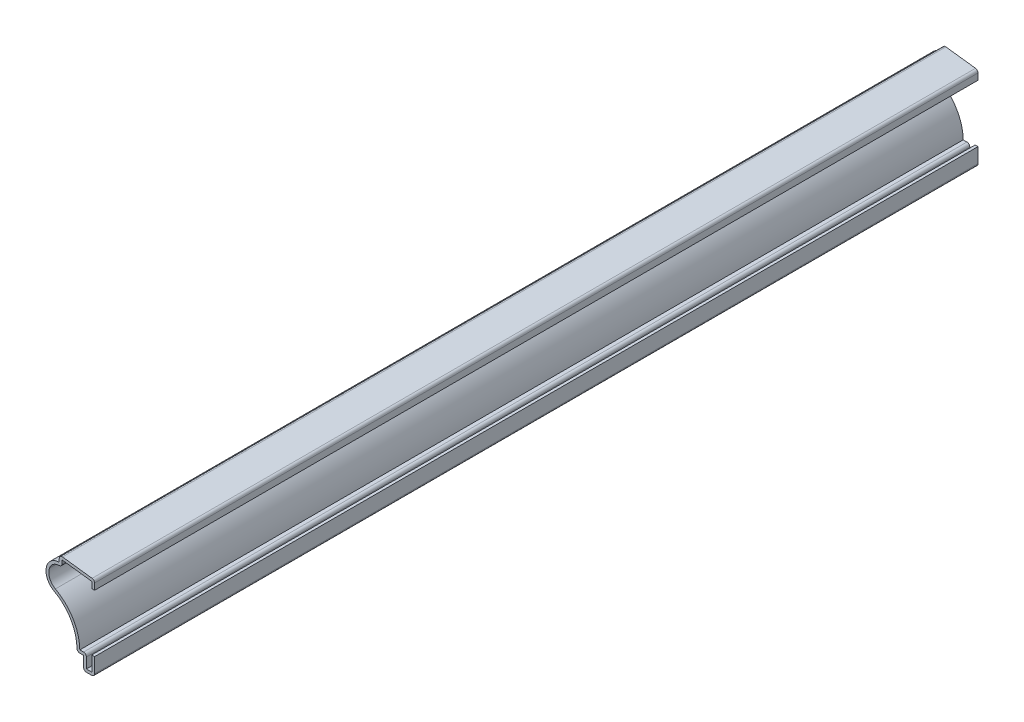
SolidWorks part; units mm, degrees
ref_plane "Front Plane" through (0, 0, 0) normal (0, 0, 1) x (1, 0, 0)
ref_plane "Top Plane" through (0, 0, 0) normal (0, 1, 0) x (1, 0, 0)
ref_plane "Right Plane" through (0, 0, 0) normal (1, 0, 0) x (0, 0, -1)
sketch "Sketch1" plane through (0, 0, 0) normal (0, 0, 1) x (1, 0, 0)
  line L0 (0, 6.35) -> (0, 0)
  line L1 (0, 0) -> (-3.9688, 0)
  line L2 (-3.9688, 0) -> (-3.9688, 4.7625)
  line L3 (-3.9688, 4.7625) -> (-6.35, 4.7625)
  line L4 (-12.7, 29.3687) -> (-12.7, 31.75)
  line L5 (-12.7, 31.75) -> (0, 30.1625)
  line L6 (0, 30.1625) -> (0, 26.9875)
  arc A0 (-6.35, 4.7625) -> (-14.5763, 19.4781) centre (-22.2051, 5.5562) ccw
  arc A1 (-12.7, 29.3687) -> (-17.1662, 26.1409) centre (-12.6577, 24.6064) ccw
  arc A2 (-17.1662, 26.1409) -> (-14.5763, 19.4781) centre (-11.9062, 24.3507) ccw
  point P14 (0, 0)
  point P16 (0, 0)
  dimension "D10" = 4.7625
  dimension "D11" = 5.5562
  dimension "D12" = 15.875
  dimension "D13" = 17.4625
  dimension "D1" = 31.75
  dimension "D2" = 4.7625
  dimension "D3" = 2.3813
  dimension "D4" = 3.175
  dimension "D5" = 1.5875
  dimension "D6" = 6.35
  dimension "D7" = 3.9688
  dimension "D8" = 2.3813
  dimension "D9" = 12.7
  dimension "D14" = 0.7937
extrude "Extrude-Thin1" add sketch "Sketch1" against normal blind 317.5 thin
fillet "Fillet1" radius 1.016 7 edges at (-6.35, 4.7625, -158.75) (0, 0, -158.75) (-3.9688, 0, -158.75) (-2.9527, 5.7785, -158.75) (-11.684, 28.2242, -158.75) (-12.7, 31.75, -158.75) (0, 30.1625, -158.75)
